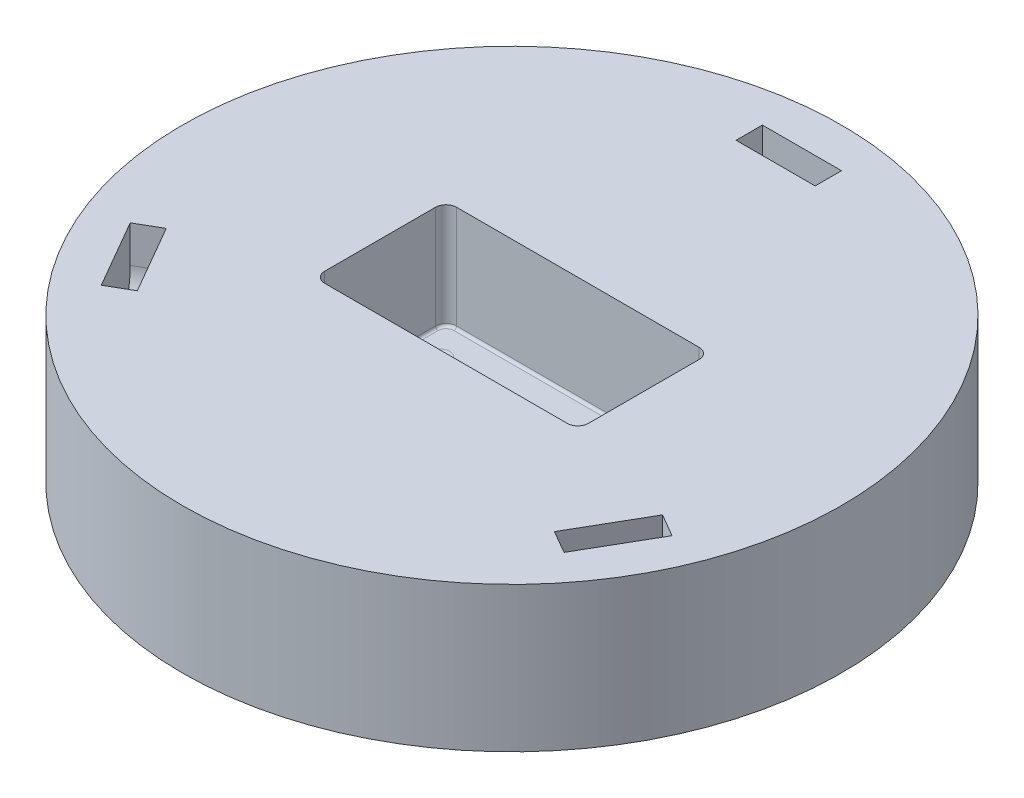
SolidWorks part; units mm, degrees
ref_plane "Front Plane" through (0, 0, 0) normal (0, 0, 1) x (1, 0, 0)
ref_plane "Top Plane" through (0, 0, 0) normal (0, 1, 0) x (1, 0, 0)
ref_plane "Right Plane" through (0, 0, 0) normal (1, 0, 0) x (0, 0, -1)
sketch "Sketch1" plane through (1517.7928, 0, 847.4958) normal (0, 1, 0) x (0.8654, 0, 0.501)
  circle A9 centre (-337.335, -781.7024) radius 79.375
  dimension "D1" = 158.75
extrude "Boss-Extrude1" add sketch "Sketch1" along normal mid plane 34.925
sketch "Sketch3" plane through (0, 17.4625, 0) normal (0, 1, 0) x (1, 0, 0)
  line L0 (802.4603, -1339.1329) -> (865.9603, -1370.8829) construction
  line L1 (802.4603, -1339.1329) -> (865.9603, -1339.1329)
  line L2 (802.4603, -1339.1329) -> (802.4603, -1370.8829)
  line L3 (802.4603, -1370.8829) -> (865.9603, -1370.8829)
  line L4 (865.9603, -1339.1329) -> (865.9603, -1370.8829)
  line L5 (802.4603, -1370.8829) -> (865.9603, -1339.1329) construction
  circle A0 centre (834.2103, -1355.0079) radius 79.375 construction
  circle A1 centre (834.2103, -1355.0079) radius 79.375 construction
  dimension "D1" = 31.75
  dimension "D2" = 63.5
extrude "Cut-Extrude1" cut sketch "Sketch3" against normal blind 25.4
hole_wizard "CBORE for M3 SHCS1" positions "Sketch6" profile "Sketch7" counterbore size "M3" standard "ANSI Metric" end condition through all
sketch "Sketch6" plane through (0, -17.4625, 0) normal (0, -1, 0) x (-1, 0, 0)
  line L1 (-859.6103, -1362.9454) -> (-808.8103, -1362.9454) construction
  line L2 (-859.6103, -1362.9454) -> (-859.6103, -1347.0704) construction
  line L3 (-859.6103, -1347.0704) -> (-808.8103, -1347.0704) construction
  line L4 (-808.8103, -1362.9454) -> (-808.8103, -1347.0704) construction
  line L5 (-859.6103, -1347.0704) -> (-808.8103, -1362.9454) construction
  circle A0 centre (-834.2103, -1355.0079) radius 79.375 construction
  circle A1 centre (-834.2103, -1355.0079) radius 79.375 construction
  point P0 (-859.6103, -1362.9454)
  point P2 (-808.8103, -1347.0704)
  point P4 (-859.6103, -1362.9454)
  point P7 (-859.6103, -1347.0704)
  point P9 (-808.8103, -1362.9454)
  dimension "D1" = 50.8
  dimension "D2" = 15.875
sketch "Sketch7" plane through (859.6103, -17.4625, 1362.9454) normal (1, 0, 0) x (0, 0, -1)
  line L0 (0, 0) -> (0, 34.925)
  line L1 (0, 34.925) -> (1.8, 34.925)
  line L3 (1.8, 34.925) -> (1.8, 3)
  line L4 (3.25, 3) -> (1.8, 3)
  line L5 (3.25, 3) -> (3.25, 0.025)
  line L6 (3.25, 0.025) -> (3.275, 0)
  line L7 (3.275, 0) -> (0, 0)
  line L8 (-3.25, 0.025) -> (-3.275, 0) construction
  line L11 (0, -6.35) -> (0, 107.95) construction
  dimension "Thru Hole Dia." = 3.6
  dimension "Thru Hole Depth" = 34.925
  dimension "C'Bore Dia." = 6.5
  dimension "C'Bore Depth" = 3
  dimension "Near C'Sink Dia." = 6.55
  dimension "Near C'Sink Angle" = 90
fillet "Fillet1" radius 2.54 4 edges at (802.4603, 4.7625, 1339.1329) (802.4603, 4.7625, 1370.8829) (865.9603, 4.7625, 1370.8829) (865.9603, 4.7625, 1339.1329)
fillet "Fillet2" radius 0.635 12 edges at (865.2164, -7.9375, 1339.8768) (865.9603, -7.9375, 1355.0079) (865.2164, -7.9375, 1370.1389) (834.2103, -7.9375, 1370.8829) (803.2043, -7.9375, 1370.1389) (802.4603, -7.9375, 1355.0079) (803.2043, -7.9375, 1339.8768) (834.2103, -7.9375, 1339.1329) (808.8103, -7.9375, 1364.7454) (859.6103, -7.9375, 1348.8704) (859.6103, -7.9375, 1364.7454) (808.8103, -7.9375, 1348.8704)
ref_plane "Plane1" through (0, 0, 1288.3329) normal (0, 0, 1) x (1, 0, 0)
sketch "Sketch8" plane through (0, 0, 1288.3329) normal (0, 0, 1) x (1, 0, 0)
  line L0 (843.7353, 8.5725) -> (843.7353, 17.4625)
  line L1 (913.5853, 17.4625) -> (754.8353, 17.4625) construction
  line L2 (843.7353, 17.4625) -> (824.6853, 17.4625)
  line L3 (824.6853, 17.4625) -> (824.6853, 8.5725)
  line L4 (834.2103, -17.4625) -> (834.2103, 17.4625) construction
  line L5 (754.8353, -17.4625) -> (913.5853, -17.4625) construction
  arc A0 (824.6853, 8.5725) -> (843.7353, 8.5725) centre (834.2103, 8.5725) ccw
  dimension "D1" = 9.525
  dimension "D2" = 8.89
extrude "Cut-Extrude2" cut sketch "Sketch8" against normal mid plane 6.35
pattern_circular "CirPattern1" count 3 every 120 about axis through (834.2103, 0, 1355.0079) along (0, 1, 0) of "Cut-Extrude2"
sketch "Sketch9" plane through (0, -17.4625, 0) normal (0, -1, 0) x (1, 0, 0)
  line L7 (881.8353, 1402.6329) -> (786.5853, 1402.6329) construction
  line L8 (881.8353, 1402.6329) -> (881.8353, 1307.3829) construction
  line L9 (881.8353, 1307.3829) -> (786.5853, 1307.3829) construction
  line L10 (786.5853, 1402.6329) -> (786.5853, 1307.3829) construction
  line L11 (881.8353, 1402.6329) -> (786.5853, 1307.3829) construction
  line L12 (881.8353, 1307.3829) -> (786.5853, 1402.6329) construction
  circle A0 centre (881.8353, 1307.3829) radius 2.75
  circle A1 centre (786.5853, 1307.3829) radius 2.75
  circle A2 centre (786.5853, 1402.6329) radius 2.75
  circle A3 centre (881.8353, 1402.6329) radius 2.75
  point P5 (834.2103, 1355.0079)
  dimension "D2" = 5.5
  dimension "D1" = 95.25
  dimension "D3" = 2
  dimension "D4" = 2
extrude "Cut-Extrude3" cut sketch "Sketch9" against normal blind 8
